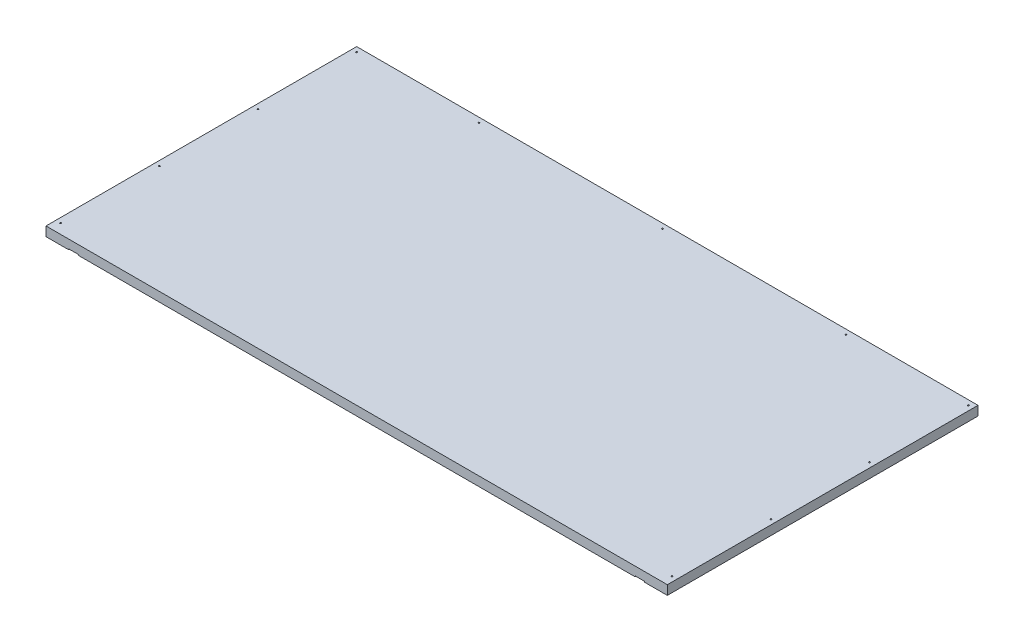
SolidWorks part; units mm, degrees
material "Cedar"
ref_plane "Front Plane" through (0, 0, 0) normal (0, 0, 1) x (1, 0, 0)
ref_plane "Top Plane" through (0, 0, 0) normal (0, 1, 0) x (1, 0, 0)
ref_plane "Right Plane" through (0, 0, 0) normal (1, 0, 0) x (0, 0, -1)
sketch "Sketch1" plane through (0, 0, 0) normal (0, 1, 0) x (1, 0, 0)
  line L1 (-609.6, -304.8) -> (609.6, -304.8)
  line L2 (-609.6, -304.8) -> (-609.6, 304.8)
  line L3 (-609.6, 304.8) -> (609.6, 304.8)
  line L4 (609.6, -304.8) -> (609.6, 304.8)
  line L5 (-609.6, -304.8) -> (609.6, 304.8) construction
  line L6 (-609.6, 304.8) -> (609.6, -304.8) construction
  point P0 (0, 0)
  dimension "D1" = 1219.2
  dimension "D2" = 609.6
extrude "Boss-Extrude1" add sketch "Sketch1" along normal blind 18.2562
sketch "Sketch2" plane through (0, 0, 0) normal (0, 1, 0) x (1, 0, 0)
  line L0 (609.6, 304.8) -> (-609.6, 304.8) construction
  line L1 (-565.15, 304.8) -> (-546.1, 304.8)
  line L2 (-565.15, 304.8) -> (-565.15, -304.8)
  line L3 (-565.15, -304.8) -> (-546.1, -304.8)
  line L4 (-546.1, 304.8) -> (-546.1, 9.525)
  line L5 (-609.6, -304.8) -> (609.6, -304.8) construction
  line L7 (-546.1, 9.525) -> (-120.65, 9.525)
  line L8 (-546.1, 9.525) -> (-546.1, -9.525) construction
  line L9 (-546.1, -9.525) -> (-120.65, -9.525)
  line L12 (565.15, 304.8) -> (546.1, 304.8)
  line L13 (565.15, 304.8) -> (565.15, -304.8)
  line L14 (565.15, -304.8) -> (546.1, -304.8)
  line L15 (546.1, 304.8) -> (546.1, 9.525)
  line L17 (-120.65, -9.525) -> (-101.6, -9.525)
  line L18 (-120.65, -9.525) -> (-120.65, -304.8) construction
  line L19 (-120.65, -304.8) -> (-101.6, -304.8) construction
  line L20 (-101.6, -9.525) -> (-101.6, -304.8) construction
  line L21 (-546.1, -9.525) -> (-546.1, -304.8)
  line L23 (101.6, -9.525) -> (101.6, -304.8) construction
  line L24 (101.6, -304.8) -> (120.65, -304.8) construction
  line L25 (120.65, -9.525) -> (120.65, -304.8) construction
  line L26 (-101.6, -9.525) -> (101.6, -9.525)
  line L27 (0, 0) -> (0, -9.525) construction
  line L28 (546.1, -9.525) -> (546.1, -304.8)
  line L29 (120.65, -9.525) -> (546.1, -9.525)
  line L30 (-565.15, 304.8) -> (-609.6, 304.8) construction
  line L31 (565.15, 304.8) -> (609.6, 304.8) construction
  line L32 (-609.6, 304.8) -> (-609.6, -304.8) construction
  line L33 (120.65, 9.525) -> (546.1, 9.525)
  line L35 (101.6, 9.525) -> (101.6, 304.8)
  line L36 (101.6, 304.8) -> (120.65, 304.8)
  line L37 (120.65, 9.525) -> (120.65, 304.8)
  line L38 (-546.1, 0) -> (-609.6, 0) construction
  line L39 (101.6, -9.525) -> (120.65, -9.525)
  line L40 (609.6, 304.8) -> (-609.6, 304.8) construction
  line L41 (-120.65, 304.8) -> (-101.6, 304.8)
  line L42 (-120.65, 304.8) -> (-120.65, 9.525)
  line L44 (-101.6, 304.8) -> (-101.6, 9.525)
  line L45 (-101.6, 9.525) -> (101.6, 9.525)
  dimension "D1" = 19.05
  dimension "D3" = 425.45
  dimension "D4" = 203.2
  dimension "D5" = 44.45
extrude "Cut-Extrude1" cut sketch "Sketch2" along normal blind 1.5875
sketch "Sketch5" plane through (0, 1.5875, 0) normal (0, -1, 0) x (-1, 0, 0)
  line L0 (-546.1, -9.525) -> (546.1, -9.525) construction
  point P0 (0, -9.525)
sketch "Sketch6" plane through (0, 18.2562, 0) normal (0, 1, 0) x (1, 0, 0)
  line L0 (-609.6, -304.8) -> (609.6, -304.8) construction
  line L2 (-609.6, 304.8) -> (-609.6, -304.8)
  line L3 (-609.6, -304.8) -> (-590.55, -304.8)
  line L4 (-590.55, 285.75) -> (-590.55, -304.8)
  line L5 (546.1, -304.8) -> (565.15, -304.8) construction
  line L8 (-590.55, 285.75) -> (590.55, 285.75)
  line L11 (609.6, 304.8) -> (609.6, -304.8)
  line L12 (609.6, -304.8) -> (590.55, -304.8)
  line L13 (590.55, 285.75) -> (590.55, -304.8)
  line L14 (609.6, 304.8) -> (-609.6, 304.8) construction
  line L15 (609.6, 304.8) -> (-609.6, 304.8)
  line L16 (-590.55, 285.75) -> (-590.55, 304.8) construction
  line L17 (0, 0) -> (0, 285.75)
  line L18 (0, 0) -> (0, -304.8)
sketch "Sketch8" plane through (0, 18.2562, 0) normal (0, 1, 0) x (1, 0, 0)
  line L0 (-600.075, -304.8) -> (-600.075, 295.275) construction
  line L1 (-609.6, -304.8) -> (-590.55, -304.8) construction
  line L2 (-600.075, 295.275) -> (600.075, 295.275) construction
  line L3 (600.075, 295.275) -> (600.075, -304.8) construction
  line L4 (609.6, -304.8) -> (590.55, -304.8) construction
  line L5 (-590.55, 285.75) -> (-590.55, 304.8) construction
  circle A0 centre (-600.075, -285.75) radius 1.397
  circle A5 centre (600.075, -285.75) radius 1.397
  circle A10 centre (600.075, -92.075) radius 1.397
  circle A15 centre (600.075, 101.6) radius 1.397
  circle A16 centre (-360.045, 295.275) radius 1.397
  circle A18 centre (0, 295.275) radius 1.397
  circle A19 centre (360.045, 295.275) radius 1.397
  circle A20 centre (600.075, 295.275) radius 1.397
  circle A21 centre (-600.075, -92.075) radius 1.397
  circle A22 centre (-600.075, 101.6) radius 1.397
  circle A23 centre (-600.075, 295.275) radius 1.397
  point P5 (-590.55, 295.275)
  point P9 (0, 0)
  point P14 (0, 0)
  point P15 (47.6296, 286.2111)
  point P16 (0, 295.275)
  dimension "D1" = 2.794
  dimension "D4" = 19.05
extrude "Cut-Extrude2" cut sketch "Sketch8" against normal through all
